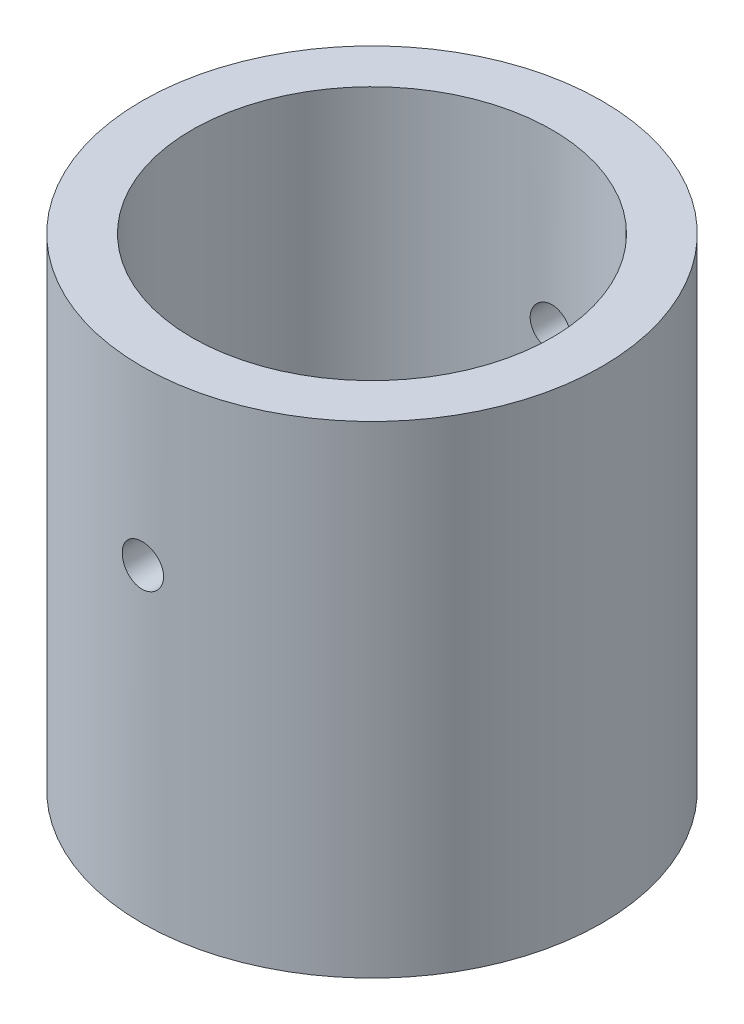
SolidWorks part; units mm, degrees
ref_plane "Front" through (0, 0, 0) normal (0, 0, 1) x (1, 0, 0)
ref_plane "Top" through (0, 0, 0) normal (0, 1, 0) x (1, 0, 0)
ref_plane "Right" through (0, 0, 0) normal (1, 0, 0) x (0, 0, -1)
sketch "Sketch1" plane through (0, 0, 0) normal (0, 1, 0) x (1, 0, 0)
  circle A0 centre (0, 0) radius 16.7005
  circle A1 centre (0, 0) radius 13.0683
  dimension "D1" = 33.401
  dimension "D2" = 26.1366
extrude "Boss-Extrude1" add sketch "Sketch1" along normal blind 25 and the other way blind 10
sketch "Sketch3" plane through (0, 0, 0) normal (0, 0, 1) x (1, 0, 0)
  line L0 (0, 0) -> (0, 25) construction
  line L1 (13.0683, 25) -> (-13.0683, 25) construction
  circle A0 centre (0, 12.5) radius 1.5
  dimension "D1" = 3
extrude "Cut-Extrude1" cut sketch "Sketch3" against normal through all both and the other way through all
